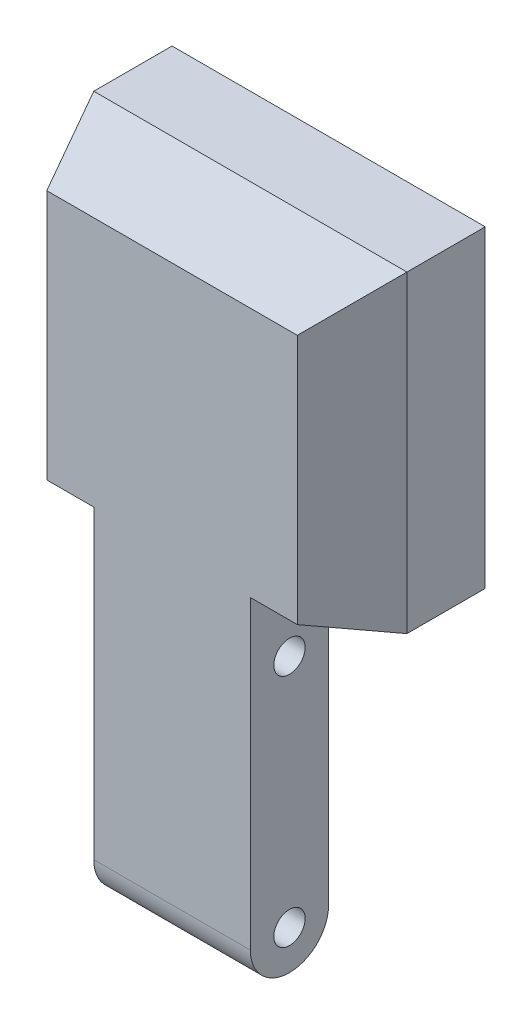
SolidWorks part; units mm, degrees
ref_plane "Alzado" through (0, 0, 0) normal (0, 0, 1) x (1, 0, 0)
ref_plane "Planta" through (0, 0, 0) normal (0, 1, 0) x (1, 0, 0)
ref_plane "Vista lateral" through (0, 0, 0) normal (1, 0, 0) x (0, 0, -1)
sketch "Croquis1" plane through (0, 0, 0) normal (0, 0, 1) x (1, 0, 0)
  line L1 (-10, -20) -> (10, -20)
  line L2 (-10, -20) -> (-10, 20)
  line L3 (-10, 20) -> (10, 20)
  line L4 (10, -20) -> (10, 20)
  line L5 (-10, -20) -> (10, 20) construction
  line L6 (-10, 20) -> (10, -20) construction
  line L7 (0, 20) -> (20, 20)
  line L8 (0, 20) -> (0, 50)
  line L9 (0, 50) -> (20, 50)
  line L10 (20, 20) -> (20, 50)
  line L11 (0, 20) -> (-20, 20)
  line L12 (0, 20) -> (0, 50)
  line L13 (0, 50) -> (-20, 50)
  line L14 (-20, 20) -> (-20, 50)
  point P0 (0, 0)
extrude "Saliente-Extruir1" add sketch "Croquis1" along normal blind 10 contours L1 L4 L3 L2 | L7 L10 L9 L8 L3 | L14 L11 L3 L8 L13
sketch "Croquis2" plane through (10, 0, 0) normal (1, 0, 0) x (0, 0, -1)
  line L0 (-5, 15) -> (-5, -15) construction
  circle A2 centre (-5, -15) radius 2
  circle A3 centre (-5, 15) radius 2
extrude "Cortar-Extruir1" cut sketch "Croquis2" against normal through all
sketch "Croquis3" plane through (0, 50, 0) normal (0, 1, 0) x (1, 0, 0)
  line L1 (20, 0) -> (-20, 0)
  line L2 (20, 0) -> (20, -10)
  line L3 (20, -10) -> (-20, -10)
  line L4 (-20, 0) -> (-20, -10)
extrude "Saliente-Extruir2" add sketch "Croquis3" along normal blind 10
sketch "Croquis4" plane through (0, 0, 10) normal (0, 0, 1) x (1, 0, 0)
  line L1 (20, 20) -> (-20, 20)
  line L2 (20, 20) -> (20, 60)
  line L3 (20, 60) -> (-20, 60)
  line L4 (-20, 20) -> (-20, 60)
extrude "Saliente-Extruir3" add sketch "Croquis4" against normal blind 20
sketch "Croquis5" plane through (0, 0, 10) normal (0, 0, 1) x (1, 0, 0)
  line L1 (-20, 20) -> (-10, 20)
  line L2 (-20, 20) -> (-20, 24)
  line L3 (-20, 24) -> (-10, 24)
  line L4 (-10, 20) -> (-10, 24)
  line L5 (20, 20) -> (10, 20)
  line L6 (20, 20) -> (20, 24)
  line L7 (20, 24) -> (10, 24)
  line L8 (10, 20) -> (10, 24)
sketch "Croquis6" plane through (20, 0, 0) normal (1, 0, 0) x (0, 0, -1)
  line L0 (-10, 20) -> (-10, 24) construction
  line L1 (-10, 20) -> (0, 20)
  line L2 (-10, 20) -> (-10, 24)
  line L5 (-10, 20) -> (0, 20) construction
  line L6 (0, 20) -> (-10, 24)
extrude "Cortar-Extruir3" cut sketch "Croquis6" against normal blind 10
sketch "Croquis7" plane through (-20, 0, 0) normal (-1, 0, 0) x (0, 0, 1)
  line L0 (0, 20) -> (10, 24)
  line L1 (10, 20) -> (0, 20)
  line L2 (10, 20) -> (10, 24)
extrude "Cortar-Extruir4" cut sketch "Croquis7" against normal blind 10
sketch "Croquis8" plane through (20, 0, 0) normal (1, 0, 0) x (0, 0, -1)
  line L0 (-10, 56) -> (0, 60)
  line L1 (-10, 60) -> (0, 60)
  line L2 (-10, 60) -> (-10, 56)
extrude "Cortar-Extruir5" cut sketch "Croquis8" against normal through all
sketch "Croquis9" plane through (0, 60, 0) normal (0, 1, 0) x (1, 0, 0)
  line L11 (-20, -10) -> (20, -10) construction
  line L13 (-20, 0) -> (-20, -10)
  line L14 (-20, -10) -> (-16, -10)
  line L16 (-20, 0) -> (-16, -10)
  line L18 (20, 0) -> (20, -10)
  line L19 (20, -10) -> (16, -10)
  line L21 (20, 0) -> (16, -10)
extrude "Cortar-Extruir6" cut sketch "Croquis9" against normal blind 40
sketch "Croquis10" plane through (10, 0, 0) normal (1, 0, 0) x (0, 0, -1)
  line L0 (-10, -15) -> (-10, -20)
  line L1 (-10, -20) -> (0, -20)
  line L2 (0, -20) -> (0, -15)
  arc A0 (-10, -15) -> (0, -15) centre (-5, -15) ccw
  line M4 (0, -20) -> (0, 20)
  line M6 (-10, 24) -> (-10, -20)
  line M7 (-10, -20) -> (0, -20)
extrude "Cortar-Extruir7" cut sketch "Croquis10" against normal through all contours A0 L1 M4 | A0 M6 M7
